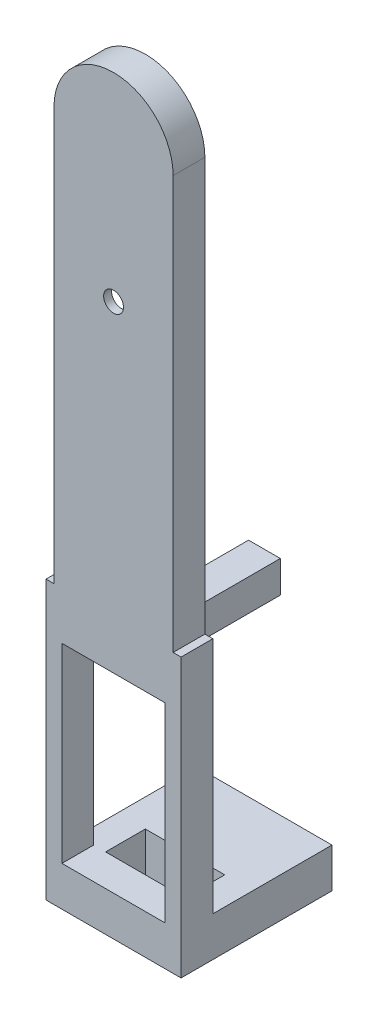
SolidWorks part; units mm, degrees
ref_plane "前基準面" through (0, 0, 0) normal (0, 0, 1) x (1, 0, 0)
ref_plane "上基準面" through (0, 0, 0) normal (0, 1, 0) x (1, 0, 0)
ref_plane "右基準面" through (0, 0, 0) normal (1, 0, 0) x (0, 0, -1)
sketch "草圖1" plane through (0, 0, 0) normal (0, 0, 1) x (1, 0, 0)
  line L0 (0, 0) -> (0, 4.6483) construction
  line L1 (7.5, 0) -> (7.5, 52)
  line L2 (7.5, 0) -> (-7.5, 0)
  line L3 (-7.5, 0) -> (-7.5, 52)
  arc A0 (7.5, 52) -> (-7.5, 52) centre (0, 52) ccw
  dimension "D1" = 7.5
  dimension "D2" = 52
extrude "填料-伸長1" add sketch "草圖1" along normal blind 4
sketch "草圖3" plane through (0, 0, 0) normal (0, 0, 1) x (1, 0, 0)
  line L0 (0, 0) -> (0, 14.8578) construction
  line L1 (7.5, 52) -> (-7.5, 52) construction
  line L2 (7.5, 15) -> (-7.5, 15) construction
  line L3 (7.5, 0) -> (7.5, 52) construction
  line L4 (-7.5, 52) -> (-7.5, 0) construction
  line L6 (7.5, 34.5) -> (5, 34.5) construction
  line L7 (5, 34.5) -> (2.1147, 16.658)
  line L8 (5, 34.5) -> (2.1328, 52)
  line L9 (-2.1328, 52) -> (-5, 34.5)
  line L10 (-5, 34.5) -> (-2.1422, 17)
  line L11 (0, 54.1328) -> (0, 59.5) construction
  line L12 (-5, 34.5) -> (-7.5, 34.5) construction
  arc A0 (7.5, 52) -> (-7.5, 52) centre (0, 52) ccw construction
  arc A1 (-4.7386, 36.0956) -> (-4.7403, 32.9094) centre (0, 34.5) ccw
  arc A2 (-2.1422, 17) -> (2.1147, 16.658) centre (0, 17) ccw
  arc A3 (-2.1328, 52) -> (2.1328, 52) centre (0, 52) cw
  arc A4 (4.7452, 32.9241) -> (4.7386, 36.0956) centre (0, 34.5) ccw
  dimension "D4" = 10
  dimension "D1" = 35
extrude "除料-伸長1" cut sketch "草圖3" along normal blind 3 contours A3 L9 L10 A2 L7 L8
sketch "草圖5" plane through (0, 0, 0) normal (0, 0, 1) x (1, 0, 0)
  line L0 (5, 34.5) -> (-5, 34.5) construction
  circle A0 centre (0, 34.5) radius 1.25
  dimension "D1" = 2.5
extrude "除料-伸長2" cut sketch "草圖5" along normal blind 12.4
sketch "草圖6" plane through (0, 0, 0) normal (0, 0, 1) x (1, 0, 0)
  line L0 (0, 62.3953) -> (0, -4.428) construction
  line L1 (0, -2.2) -> (0, 2.2) construction
  line L3 (8.5, 0) -> (-8.5, 0)
  line L4 (8.5, 0) -> (8.5, -35)
  line L5 (8.5, -35) -> (-8.5, -35)
  line L6 (-8.5, 0) -> (-8.5, -35)
  dimension "D1" = 17
  dimension "D2" = 8.5
  dimension "D3" = 35
extrude "填料-伸長2" add sketch "草圖6" along normal blind 4
sketch "草圖7" plane through (0, 0, 0) normal (0, 0, 1) x (1, 0, 0)
  line L0 (0, 64.1958) -> (0, -38.5274) construction
  line L1 (0, -2.2) -> (0, 2.2) construction
  line L3 (-6.5, -6) -> (6.5, -6)
  line L4 (-6.5, -6) -> (-6.5, -30)
  line L5 (-6.5, -30) -> (6.5, -30)
  line L6 (6.5, -6) -> (6.5, -30)
  line L7 (-8.5, -35) -> (8.5, -35) construction
  dimension "D1" = 6.5
  dimension "D2" = 13
  dimension "D3" = 24
  dimension "D4" = 5
extrude "除料-伸長3" cut sketch "草圖7" along normal blind 12.1
sketch "草圖8" plane through (0, 0, 0) normal (0, 0, 1) x (1, 0, 0)
  line L0 (0, 64.1958) -> (0, -34.8274) construction
  line L1 (0, -2.2) -> (0, 2.2) construction
  line L2 (0, 64.1958) -> (0, -39.0142) construction
  line L3 (6.5, -18) -> (-6.5, -18) construction
  line L4 (6.5, -30) -> (6.5, -6) construction
  line L5 (-6.5, -6) -> (-6.5, -30) construction
  line L6 (6.5, -6) -> (-6.5, -6) construction
  line L7 (2, -2) -> (-2, -2)
  line L8 (2, -2) -> (2, -6)
  line L9 (2, -6) -> (-2, -6)
  line L10 (-2, -2) -> (-2, -6)
  circle A0 centre (0, -4) radius 1.15
  dimension "D5" = 2.3
  dimension "D1" = 4
  dimension "D2" = 4
  dimension "D3" = 2
  dimension "D4" = 2
extrude "填料-伸長3" add sketch "草圖8" against normal blind 15
ref_plane "平面1" through (0, -35, 0) normal (0, 1, 0) x (1, 0, 0)
sketch "草圖9" plane through (0, -35, 0) normal (0, 1, 0) x (1, 0, 0)
  line L0 (0, 15.9246) -> (0, -4.8463) construction
  line L1 (0, -10.45) -> (0, 10.45) construction
  line L2 (-5, 0) -> (-5, 5)
  line L3 (7.5, 0) -> (-7.5, 0) construction
  line L4 (-5, 5) -> (5, 5)
  line L5 (-5, 0) -> (5, 0)
  line L6 (5, 0) -> (5, 5)
  line L12 (-8.5, 0) -> (8.5, 0)
  line L16 (8.5, 0) -> (8.5, 15)
  line L17 (8.5, 15) -> (-8.5, 15)
  line L19 (-8.5, 15) -> (-8.5, 0)
  point P12 (0, 0)
  point P13 (0, 5)
  point P20 (0, 0)
  point P21 (0, 15)
  point P25 (0, 0)
  point P26 (0, 15)
  dimension "D1" = 5
  dimension "D2" = 5
  dimension "D3" = 5
extrude "填料-伸長4" add sketch "草圖9" along normal blind 5
sketch "草圖10" plane through (0, 0, -15) normal (0, 0, -1) x (-1, 0, 0)
  line L0 (0, 0) -> (0, -35) construction
  line L1 (8.5, -35) -> (-8.5, -35) construction
  line L5 (8.538, -32.5) -> (-8.538, -32.5) construction
  circle A0 centre (0, -32.5) radius 1.15
  dimension "D2" = 2.3
  dimension "D1" = 2.5
extrude "除料-伸長4" cut sketch "草圖10" against normal blind 12.7 contours A0
